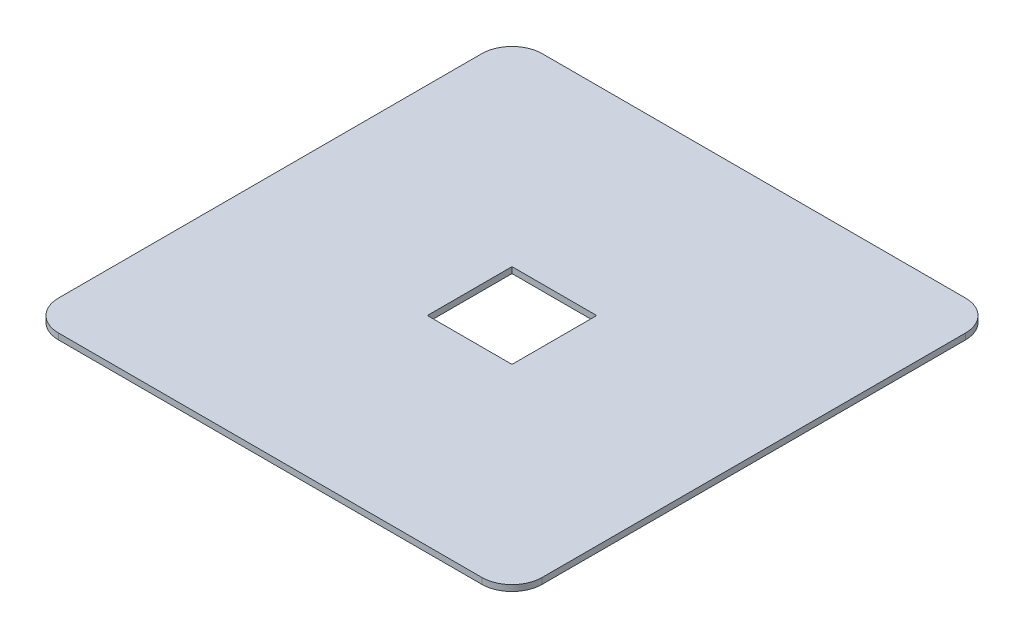
SolidWorks part; units mm, degrees
ref_plane "Face" through (0, 0, 0) normal (0, 0, 1) x (1, 0, 0)
ref_plane "Dessus" through (0, 0, 0) normal (0, 1, 0) x (1, 0, 0)
ref_plane "Droite" through (0, 0, 0) normal (1, 0, 0) x (0, 0, -1)
sketch "Esquisse1" plane through (0, 0, 0) normal (0, 1, 0) x (1, 0, 0)
  line L1 (0, 0) -> (80, 0)
  line L2 (0, 0) -> (0, 80)
  line L3 (0, 80) -> (80, 80)
  line L4 (80, 0) -> (80, 80)
  dimension "D1" = 80
  dimension "D2" = 80
extrude "Extrusion1" add sketch "Esquisse1" along normal blind 1
fillet "Congé1" radius 5 4 edges at (80, 0.5, 0) (80, 0.5, -80) (0, 0.5, -80) (0, 0.5, 0)
sketch "Esquisse2" plane through (0, 1, 0) normal (0, 1, 0) x (1, 0, 0)
  line L0 (75, 80) -> (5, 80) construction
  line L1 (33, 47) -> (47, 47)
  line L2 (33, 47) -> (33, 33)
  line L3 (33, 33) -> (47, 33)
  line L4 (47, 47) -> (47, 33)
  line L5 (80, 5) -> (80, 75) construction
  dimension "D1" = 14
  dimension "D2" = 14
  dimension "D3" = 33
  dimension "D4" = 33
extrude "Enlèv. mat.-Extru.1" cut sketch "Esquisse2" against normal through all
